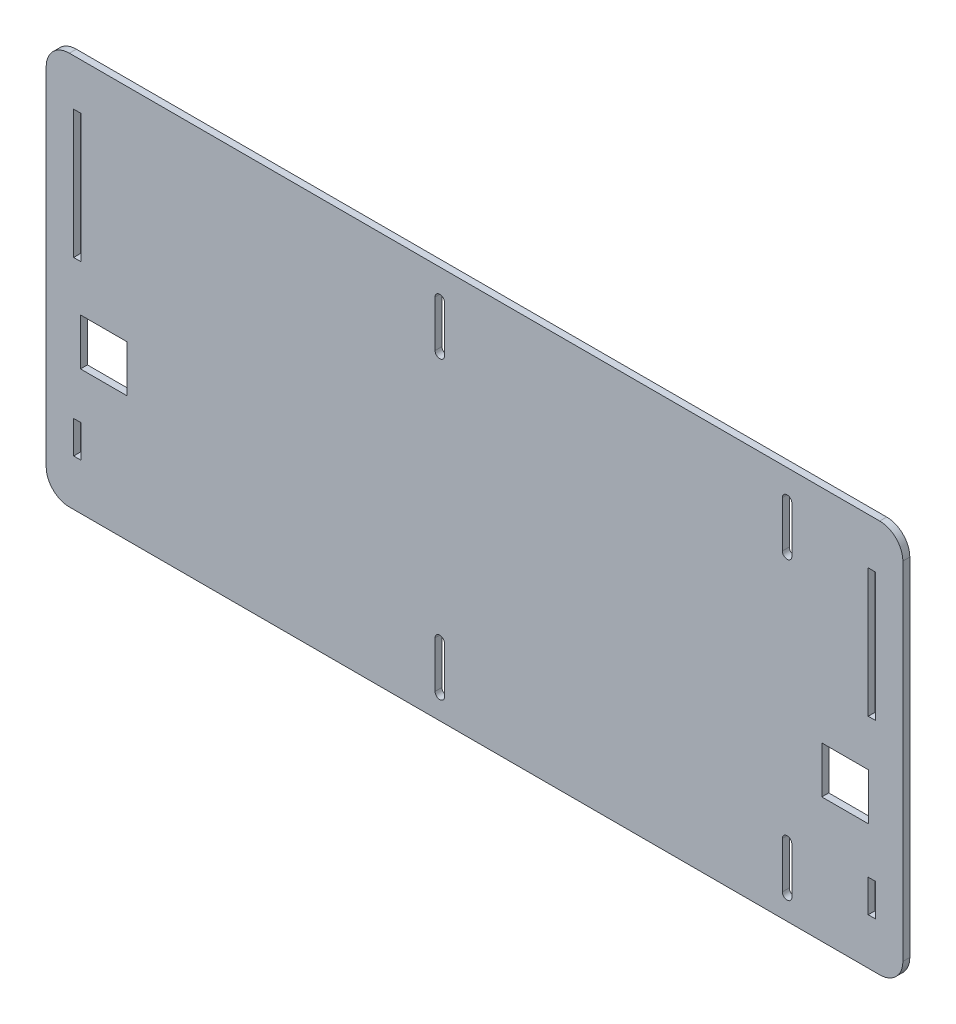
SolidWorks part; units mm, degrees
ref_plane "Front Plane" through (0, 0, 0) normal (0, 0, 1) x (1, 0, 0)
ref_plane "Top Plane" through (0, 0, 0) normal (0, 1, 0) x (1, 0, 0)
ref_plane "Right Plane" through (0, 0, 0) normal (1, 0, 0) x (0, 0, -1)
sketch "Sketch1" plane through (0, 0, 0) normal (0, 0, 1) x (1, 0, 0)
  line L0 (465.5033, 74.75) -> (430.5736, 74.75) construction
  line L1 (625, -105) -> (255, -105)
  line L2 (625, -105) -> (625, 64.75)
  line L3 (625, 64.75) -> (255, 64.75)
  line L4 (255, -105) -> (255, 64.75)
  line L5 (20, -115) -> (980, -115) construction
  line L6 (575, -85) -> (425, -85) construction
  line L7 (427.05, 52.5) -> (427.05, 32.5)
  line L8 (422.95, 52.5) -> (422.95, 32.5)
  line L9 (572.95, 52.5) -> (572.95, 32.5)
  line L10 (577.05, 52.5) -> (577.05, 32.5)
  line L11 (427.05, -75) -> (427.05, -95)
  line L12 (422.95, -75) -> (422.95, -95)
  line L13 (572.95, -75) -> (572.95, -95)
  line L14 (577.05, -95) -> (577.05, -75)
  line L15 (422.95, 42.5) -> (427.05, 42.5) construction
  line L16 (572.95, 42.5) -> (577.05, 42.5) construction
  arc A9 (422.95, 52.5) -> (427.05, 52.5) centre (425, 52.5) cw
  arc A10 (422.95, 32.5) -> (427.05, 32.5) centre (425, 32.5) ccw
  arc A11 (422.95, -75) -> (427.05, -75) centre (425, -75) cw
  arc A12 (422.95, -95) -> (427.05, -95) centre (425, -95) ccw
  arc A13 (577.05, -95) -> (572.95, -95) centre (575, -95) cw
  arc A14 (572.95, -75) -> (577.05, -75) centre (575, -75) cw
  arc A15 (572.95, 32.5) -> (577.05, 32.5) centre (575, 32.5) ccw
  arc A16 (577.05, 52.5) -> (572.95, 52.5) centre (575, 52.5) ccw
  circle A17 centre (425, 42.5) radius 2.15 construction
  circle A18 centre (575, 42.5) radius 2.15 construction
  point P8 (500, -85)
  point P39 (425, 42.5)
  point P42 (575, 42.5)
  point P43 (427.05, -85)
  point P48 (572.95, -85)
  dimension "D3" = 125
  dimension "D1" = 10
  dimension "D2" = 10
  dimension "D4" = 245
  dimension "D5" = 4.1
  dimension "D6" = 20
extrude "Boss-Extrude1" add sketch "Sketch1" along normal blind 3
sketch "Sketch3" plane through (0, 0, 3) normal (0, 0, 1) x (1, 0, 0)
  line L0 (625, 64.75) -> (255, 64.75) construction
  line L1 (269.8, -30.75) -> (290, -30.75)
  line L2 (269.8, -30.75) -> (269.8, -50.95)
  line L3 (269.8, -50.95) -> (290, -50.95)
  line L4 (290, -30.75) -> (290, -50.95)
  line L5 (590, -30.75) -> (610.2, -30.75)
  line L6 (590, -30.75) -> (590, -50.95)
  line L7 (590, -50.95) -> (610.2, -50.95)
  line L8 (610.2, -30.75) -> (610.2, -50.95)
  line L9 (427.05, -85) -> (572.95, -85) construction
  line L10 (427.05, -95) -> (427.05, -75) construction
  line L11 (572.95, -75) -> (572.95, -95) construction
  point P8 (279.9, -30.75)
  point P17 (500, -85)
  dimension "D1" = 20.2
  dimension "D2" = 95.5
  dimension "D3" = 210
  dimension "D4" = 90
extrude "Cut-Extrude1" cut sketch "Sketch3" against normal through all
sketch "Sketch4" plane through (0, 0, 3) normal (0, 0, 1) x (1, 0, 0)
  line L1 (266.85, 44.75) -> (269.95, 44.75)
  line L2 (266.85, 44.75) -> (266.85, -10.75)
  line L3 (266.85, -10.75) -> (269.95, -10.75)
  line L4 (269.95, 44.75) -> (269.95, -10.75)
  line L5 (269.95, -70.95) -> (266.85, -70.95)
  line L6 (269.95, -70.95) -> (269.95, -85)
  line L7 (269.95, -85) -> (266.85, -85)
  line L8 (266.85, -70.95) -> (266.85, -85)
  line L9 (610.05, -70.95) -> (613.15, -70.95)
  line L10 (610.05, -70.95) -> (610.05, -85)
  line L11 (610.05, -85) -> (613.15, -85)
  line L12 (613.15, -70.95) -> (613.15, -85)
  line L13 (613.15, -10.75) -> (610.05, -10.75)
  line L14 (613.15, -10.75) -> (613.15, 44.75)
  line L15 (613.15, 44.75) -> (610.05, 44.75)
  line L16 (610.05, -10.75) -> (610.05, 44.75)
  line L18 (255, -105) -> (625, -105) construction
  line L19 (269.8, -50.95) -> (290, -50.95) construction
  line L20 (290, -30.75) -> (269.8, -30.75) construction
  line L21 (625, 64.75) -> (255, 64.75) construction
  line L24 (610.2, -50.95) -> (610.2, -30.75) construction
  line L25 (269.8, -30.75) -> (269.8, -50.95) construction
  dimension "D1" = 20
  dimension "D2" = 3.1
  dimension "D3" = 20
  dimension "D4" = 20
  dimension "D5" = 20
  dimension "D6" = 0.15
  dimension "D7" = 0.15
extrude "Cut-Extrude2" cut sketch "Sketch4" against normal through all
fillet "Fillet1" radius 10 4 edges at (255, -105, 1.5) (625, -105, 1.5) (625, 64.75, 1.5) (255, 64.75, 1.5)
